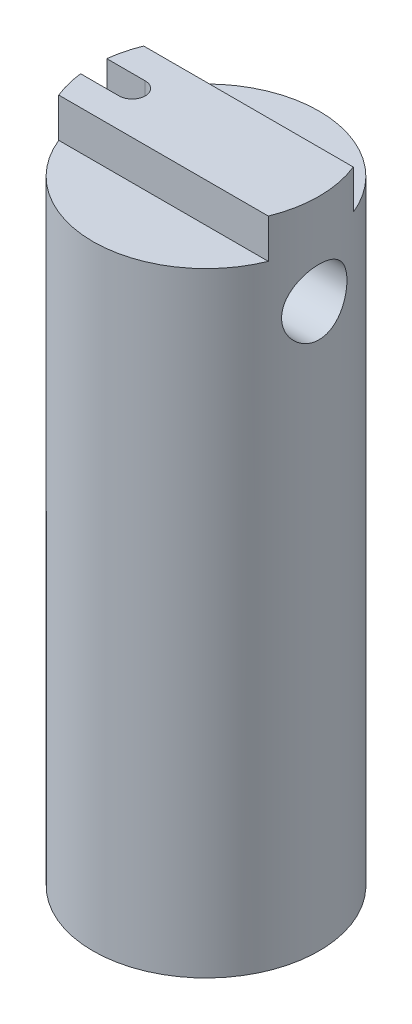
SolidWorks part; units mm, degrees
material "AISI 1020"
ref_plane "Спереди" through (0, 0, 0) normal (0, 0, 1) x (1, 0, 0)
ref_plane "Сверху" through (0, 0, 0) normal (0, 1, 0) x (1, 0, 0)
ref_plane "Справа" through (0, 0, 0) normal (1, 0, 0) x (0, 0, -1)
sketch "Эскиз1" plane through (0, 0, 0) normal (0, 1, 0) x (1, 0, 0)
  circle A0 centre (0, 0) radius 8.65 construction
  circle A1 centre (0, 0) radius 8.65
extrude "Бобышка-Вытянуть1" add sketch "Эскиз1" against normal blind 50
sketch "Эскиз2" plane through (0, -50, 0) normal (0, -1, 0) x (1, 0, 0)
  line L0 (-5.65, 0) -> (-8.65, 0) construction
  line L1 (0.0148, 0) -> (-17.0651, 0) construction
  line L2 (-5.65, -3) -> (-8.65, -3)
  line L3 (-5.65, 3) -> (-8.65, 3)
  circle A0 centre (0, 0) radius 8.65 construction
  arc A1 (-5.65, -3) -> (-5.65, 3) centre (-5.65, 0) ccw
  arc A2 (-8.65, 3) -> (-8.65, -3) centre (-8.65, 0) ccw
  point P7 (-7.15, 0)
  dimension "D1" = 6
  dimension "D2" = 3
extrude "Вырез-Вытянуть1" cut sketch "Эскиз2" against normal up to vertex (40 mm away)
sketch "Эскиз3" plane through (0, 0, 0) normal (0, -1, 0) x (1, 0, 0)
  line L0 (-5.65, 0) -> (-8.65, 0) construction
  line L1 (-36.3091, 0) -> (-5.65, 0) construction
  line L2 (-5.65, -1) -> (-8.65, -1)
  line L3 (-5.65, 1) -> (-8.65, 1)
  arc A1 (-5.65, -1) -> (-5.65, 1) centre (-5.65, 0) ccw
  arc A2 (-8.65, 1) -> (-8.65, -1) centre (-8.65, 0) ccw
  arc A3 (-5.65, -3) -> (-5.65, 3) centre (-5.65, 0) ccw construction
  circle A4 centre (0, 0) radius 8.65 construction
  point P7 (-7.15, 0)
  dimension "D1" = 2
extrude "Вырез-Вытянуть2" cut sketch "Эскиз3" along normal through all
sketch "Эскиз4" plane through (0, 0, 0) normal (1, 0, 0) x (0, 0, -1)
  line L0 (0, -1000) -> (0, 49000) construction
  line L1 (3.25, -3) -> (3.25, 0)
  line L2 (-3.25, -3) -> (-10.65, -3)
  line L3 (-3.25, -3) -> (-3.25, 0)
  line L4 (-3.25, 0) -> (-10.65, 0)
  line L5 (-10.65, -3) -> (-10.65, 0)
  line L6 (3.25, 0) -> (10.65, 0)
  line L7 (10.65, -3) -> (10.65, 0)
  line L8 (3.25, -3) -> (10.65, -3)
  line L9 (8.65, 0) -> (-8.65, 0) construction
  line L10 (-8.65, 0) -> (-8.65, -50) construction
  dimension "D1" = 2
extrude "Вырез-Вытянуть3" cut sketch "Эскиз4" against normal through all both and the other way through all
ref_plane "Плоскость1" through (8.65, 0, 0) normal (1, 0, 0) x (0, 0, -1)
sketch "Эскиз5" plane through (8.65, 0, 0) normal (1, 0, 0) x (0, 0, -1)
  line L0 (0, 13.3669) -> (0, -38.2097) construction
  line L1 (-7.2879, -13) -> (7.2879, -13) construction
  circle A0 centre (0, -7) radius 3
  dimension "D1" = 6
  dimension "D2" = 6
hole_wizard "Отверстие обработанное метчиком M61" positions "Эскиз6" profile "Эскиз7" tap size "M6" standard "ISO"
sketch "Эскиз6" plane through (8.65, 0, 0) normal (1, 0, 0) x (0, 0, -1)
  point P0 (0, -7)
sketch "Эскиз7" plane through (8.65, -7, 0) normal (0, 1, 0) x (0, 0, -1)
  line L0 (0, 0) -> (0, 6.5022)
  line L1 (0, 6.5022) -> (2.5, 5)
  line L2 (2.5, 5) -> (2.5, 0)
  line L5 (2.5, 0) -> (0, 0)
  line L10 (0, 6.5022) -> (-2.5, 5) construction
  line L11 (0, -6.35) -> (0, 107.95) construction
  dimension "Диаметр сверла" = 5
  dimension "Глубина сверла" = 5
  dimension "Угол заточки сверла" = 118
cosmetic thread "Отверстие резьбы1" parameters "D1"=5, "D2"=6
